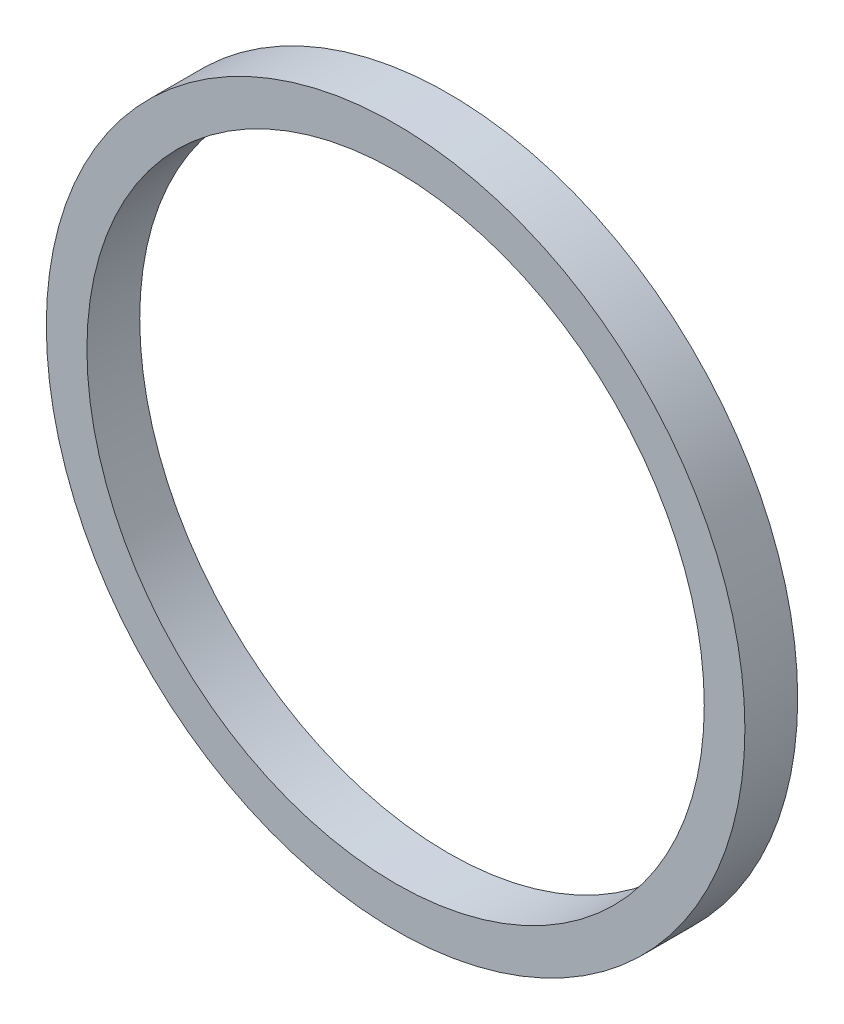
SolidWorks part; units mm, degrees
material "Silicon"
ref_plane "Front" through (0, 0, 0) normal (0, 0, 1) x (1, 0, 0)
ref_plane "Top" through (0, 0, 0) normal (0, 1, 0) x (1, 0, 0)
ref_plane "Right" through (0, 0, 0) normal (1, 0, 0) x (0, 0, -1)
sketch "Sketch1" plane through (0, 0, 0) normal (0, 0, 1) x (1, 0, 0)
  circle A0 centre (0, 0) radius 86
  circle A1 centre (0, 0) radius 76
extrude "Boss-Extrude1" add sketch "Sketch1" along normal blind 13
